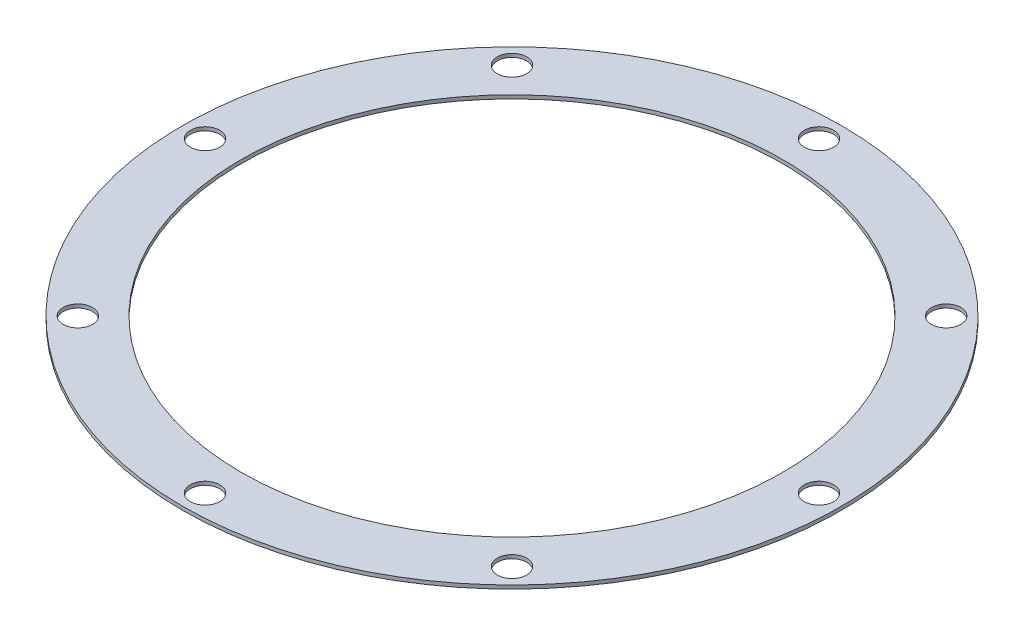
SolidWorks part; units mm, degrees
material "NBR"
ref_plane "Front Plane" through (0, 0, 0) normal (0, 0, 1) x (1, 0, 0)
ref_plane "Top Plane" through (0, 0, 0) normal (0, 1, 0) x (1, 0, 0)
ref_plane "Right Plane" through (0, 0, 0) normal (1, 0, 0) x (0, 0, -1)
sketch "Sketch1" plane through (0, 0, 0) normal (0, 1, 0) x (1, 0, 0)
  circle A0 centre (0, 0) radius 73
  circle A1 centre (0, 0) radius 60
  circle A2 centre (-48.0833, 48.0833) radius 3.25
  circle A3 centre (-68, 0) radius 3.25
  circle A4 centre (0, 68) radius 3.25
  circle A5 centre (48.0833, 48.0833) radius 3.25
  circle A6 centre (68, 0) radius 3.25
  circle A7 centre (48.0833, -48.0833) radius 3.25
  circle A8 centre (0, -68) radius 3.25
  circle A9 centre (-48.0833, -48.0833) radius 3.25
  point P22 (0, 0)
  point P24 (0, 0)
  dimension "D1" = 146
  dimension "D2" = 120
  dimension "D3" = 68
  dimension "D4" = 6.5
  dimension "D5" = 8
extrude "Boss-Extrude1" add sketch "Sketch1" along normal blind 0.7937
